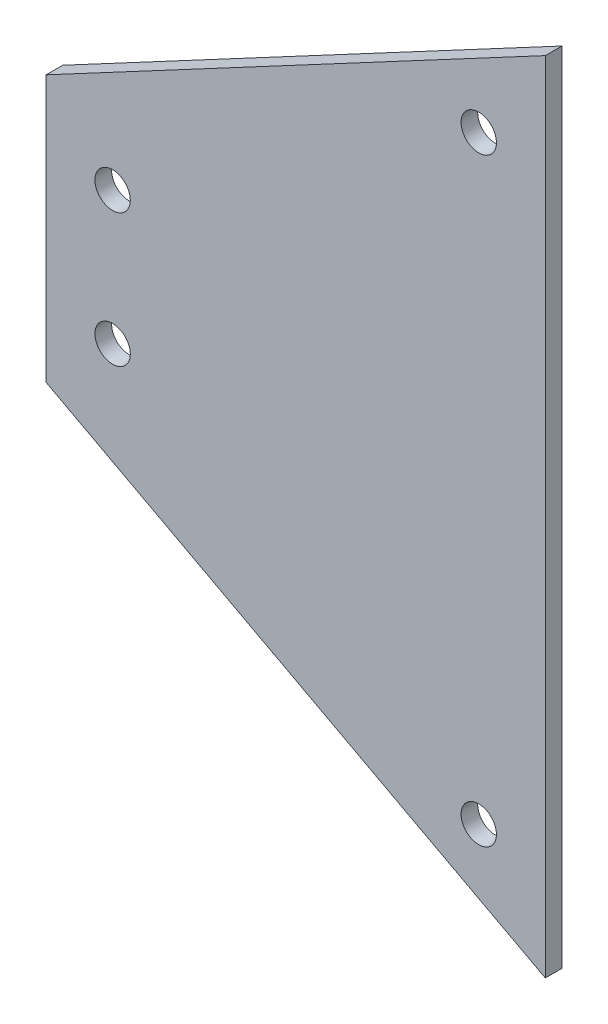
SolidWorks part; units mm, degrees
material "6061-T6 (SS)"
ref_plane "Front Plane" through (0, 0, 0) normal (0, 0, 1) x (1, 0, 0)
ref_plane "Top Plane" through (0, 0, 0) normal (0, 1, 0) x (1, 0, 0)
ref_plane "Right Plane" through (0, 0, 0) normal (1, 0, 0) x (0, 0, -1)
sketch "Sketch2" plane through (0, 0, 0) normal (0, 0, 1) x (1, 0, 0)
  line L0 (-95.25, -25.4) -> (-95.25, 25.4)
  line L1 (0, -76.2) -> (0, 76.2)
  line L2 (0, 76.2) -> (-95.25, 25.4)
  line L3 (0, 0) -> (-95.25, 0) construction
  line L4 (0, -76.2) -> (-95.25, -25.4)
  line L5 (-95.25, 25.4) -> (-95.25, 76.2)
  line L6 (-95.25, 76.2) -> (0, 76.2)
  line L7 (-95.25, -25.4) -> (-95.25, -76.2)
  line L8 (-95.25, -76.2) -> (0, -76.2)
  point P5 (-95.25, 0)
  dimension "D1" = 50.8
  dimension "D2" = 95.25
  dimension "D3" = 76.2
sketch "Sketch3" plane through (0, 0, 0) normal (0, 1, 0) x (1, 0, 0)
  line L0 (-127, 228.6) -> (-127, -228.6)
  line L1 (-95.25, 0) -> (0, 0) construction
  line L2 (-127, -228.6) -> (0, -228.6)
  line L3 (-127, 0) -> (-123.825, 0) construction
  line L4 (-123.825, 225.425) -> (-123.825, -225.425)
  line L6 (-123.825, -225.425) -> (0, -225.425)
  line L7 (0, -225.425) -> (0, -228.6)
  line L8 (0, 225.425) -> (0, 228.6)
  line L9 (-123.825, 225.425) -> (0, 225.425)
  line L10 (-127, 228.6) -> (0, 228.6)
  dimension "D1" = 127
  dimension "D2" = 3.175
  dimension "D3" = 3.175
  dimension "D4" = 225.425
extrude "Boss-Extrude3" add sketch "Sketch2" along normal mid plane 3.175 contours L3 L1 L2 L0 | L1 L3 L0 L4
sketch "Sketch4" plane through (0, 0, 0) normal (0, 0, 1) x (1, 0, 0)
  line L0 (0, -76.2) -> (0, 76.2) construction
  circle A0 centre (-39.6875, -65.0875) radius 22.225
  dimension "D1" = 44.45
  dimension "D2" = 39.6875
  dimension "D3" = 65.0875
extrude "Cut-Extrude1" [suppressed] cut sketch "Sketch4" against normal through all both and the other way through all
sketch "Sketch5" plane through (0, 0, 1.5875) normal (0, 0, 1) x (1, 0, 0)
  line L0 (-95.25, 0) -> (-122.2938, 0) construction
  line L1 (0, -76.2) -> (0, 76.2) construction
  line L4 (-95.25, -25.4) -> (-95.25, 25.4) construction
  line L5 (0, 0) -> (-36.4882, 0) construction
  circle A0 centre (-82.55, 12.7) radius 2.5797
  circle A1 centre (-82.55, -12.7) radius 2.5797
  circle A2 centre (-12.7, 57.15) radius 2.5797
  circle A3 centre (-12.7, -57.15) radius 2.5797
  dimension "D1" = 5.1594
  dimension "D2" = 114.3
  dimension "D3" = 12.7
  dimension "D4" = 12.7
  dimension "D6" = 25.4
hole_wizard "17/64 (0.26563) Diameter Hole1" positions "Sketch10" profile "Sketch11" hole size "17/64" standard "ANSI Inch" end condition through all
sketch "Sketch10" plane through (0, 0, 1.5875) normal (0, 0, 1) x (1, 0, 0)
  point P0 (-82.55, 12.7)
  point P3 (-82.55, -12.7)
  point P6 (-12.7, -57.15)
  point P9 (-12.7, 57.15)
sketch "Sketch11" plane through (-82.55, 12.7, 1.5875) normal (1, 0, 0) x (0, -1, 0)
  line L0 (0, 0) -> (0, 3.175)
  line L1 (0, 3.175) -> (3.3735, 3.175)
  line L2 (3.3735, 3.175) -> (3.3735, 0)
  line L5 (3.3735, 0) -> (0, 0)
  line L11 (0, -6.35) -> (0, 107.95) construction
  dimension "Thru Hole Dia." = 6.747
  dimension "Thru Hole Depth" = 3.175
